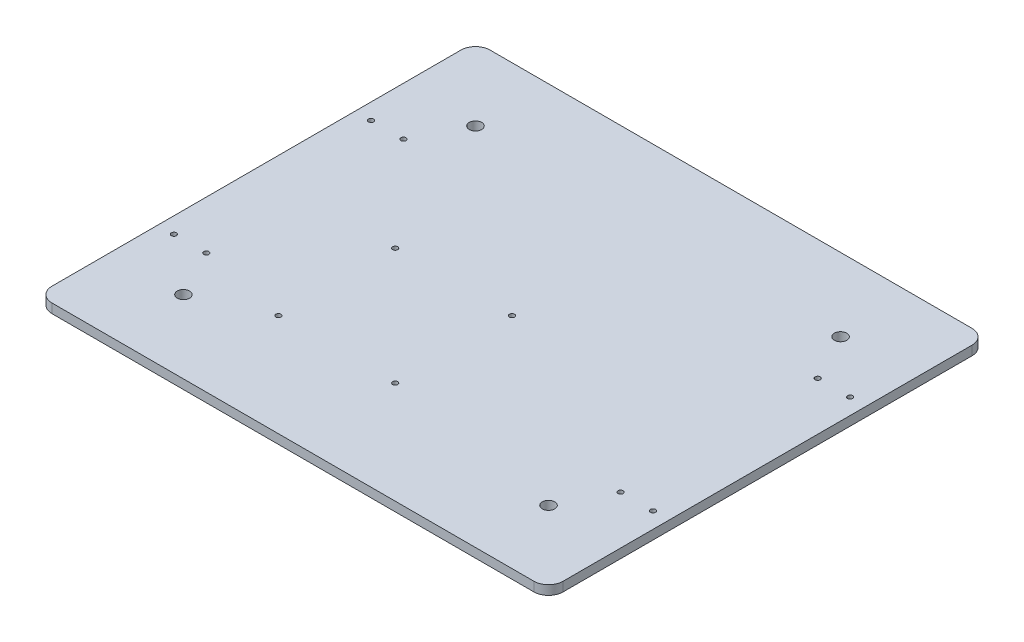
SolidWorks part; units mm, degrees
ref_plane "Front Plane" through (0, 0, 0) normal (0, 0, 1) x (1, 0, 0)
ref_plane "Top Plane" through (0, 0, 0) normal (0, 1, 0) x (1, 0, 0)
ref_plane "Right Plane" through (0, 0, 0) normal (1, 0, 0) x (0, 0, -1)
sketch "Sketch1" plane through (0, 0, 0) normal (0, 1, 0) x (1, 0, 0)
  line L0 (0, 150) -> (0, -150) construction
  line L1 (175, -150) -> (-175, -150)
  line L2 (175, -150) -> (175, 150)
  line L3 (175, 150) -> (-175, 150)
  line L4 (-175, -150) -> (-175, 150)
  line L5 (175, -150) -> (-175, 150) construction
  line L6 (175, 150) -> (-175, -150) construction
  line L7 (-175, 0) -> (175, 0) construction
  point P0 (0, 0)
  dimension "D1" = 350
  dimension "D2" = 300
extrude "Boss-Extrude1" add sketch "Sketch1" along normal blind 6.35
sketch "Sketch2" plane through (0, 0, 0) normal (0, -1, 0) x (1, 0, 0)
  line L0 (175, -150) -> (-175, -150) construction
  line L1 (-175, -150) -> (-175, 150) construction
  circle A0 centre (-125, -100) radius 4.25
  dimension "D3" = 8.5
  dimension "D1" = 50
  dimension "D2" = 50
extrude "Cut-Extrude1" cut sketch "Sketch2" against normal through all
pattern_linear "LPattern2" count 2 spacing 200 along (0, 0, 1) of "Cut-Extrude1"
pattern_linear "LPattern3" count 2 spacing 250 along (1, 0, 0) of "LPattern2", "Cut-Extrude1"
fillet "Fillet1" radius 10 4 edges at (-175, 3.175, 150) (175, 3.175, 150) (175, 3.175, -150) (-175, 3.175, -150)
sketch "Sketch3" plane through (0, 0, 0) normal (0, -1, 0) x (1, 0, 0)
  line L0 (-175, 0) -> (175, 0) construction
  line L1 (-175, -140) -> (-175, 140) construction
  line L2 (175, 140) -> (175, -140) construction
  line L3 (0, -150) -> (0, 150) construction
  line L4 (165, -150) -> (-165, -150) construction
  line L5 (-165, 150) -> (165, 150) construction
sketch "Sketch4" plane through (0, 0, 0) normal (0, -1, 0) x (1, 0, 0)
  circle A0 centre (0, 0) radius 1.75
  dimension "D1" = 3.5
extrude "Cut-Extrude2" cut sketch "Sketch4" against normal through all
pattern_linear "LPattern5" count 2 spacing 80 along (-1, 0, 0) count 2 spacing 80 along (0, 0, 1) of "Cut-Extrude2"
sketch "Sketch5" plane through (0, 0, 0) normal (0, -1, 0) x (1, 0, 0)
  line L0 (0, -150) -> (0, 150) construction
  line L1 (-175, 0) -> (175, 0) construction
  circle A0 centre (-141.82, -67.5) radius 1.75
  dimension "D1" = 141.82
  dimension "D2" = 3.5
  dimension "D3" = 67.5
extrude "Cut-Extrude3" cut sketch "Sketch5" against normal through all
pattern_linear "LPattern6" count 2 spacing 22.23 along (-1, 0, 0) count 2 spacing 135 along (0, 0, 1) of "Cut-Extrude3"
sketch "Sketch7" plane through (0, 0, 0) normal (0, -1, 0) x (1, 0, 0)
  line L0 (-175, 0) -> (175, 0) construction
  line L1 (0, -150) -> (0, 150) construction
  circle A0 centre (141.82, -67.5) radius 1.75
  dimension "D1" = 67.5
  dimension "D3" = 3.5
  dimension "D2" = 141.82
extrude "Cut-Extrude4" cut sketch "Sketch7" against normal through all
pattern_linear "LPattern9" count 2 spacing 22.23 along (1, 0, 0) count 2 spacing 135 along (0, 0, 1) of "Cut-Extrude4"
